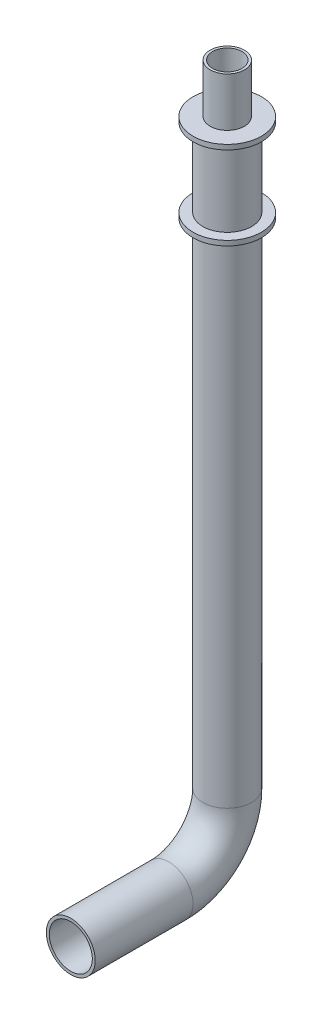
SolidWorks part; units mm, degrees
material "AISI 316 Stainless Steel Sheet (SS)"
ref_plane "Front Plane" through (0, 0, 0) normal (0, 0, 1) x (1, 0, 0)
ref_plane "Top Plane" through (0, 0, 0) normal (0, 1, 0) x (1, 0, 0)
ref_plane "Right Plane" through (0, 0, 0) normal (1, 0, 0) x (0, 0, -1)
sketch "Sketch2" plane through (0, 0, 0) normal (1, 0, 0) x (0, 0, -1)
  line L0 (-160, 0) -> (-60, 0)
  line L1 (0, 60) -> (0, 650)
  arc A0 (-60, 0) -> (0, 60) centre (-60, 60) ccw
  point P6 (0, 0)
  dimension "D3" = 60
  dimension "D1" = 650
  dimension "D2" = 160
ref_plane "Plane1" through (0, 650, 0) normal (0, 1, 0) x (1, 0, 0)
sketch "Sketch9" plane through (0, 650, 0) normal (0, 1, 0) x (1, 0, 0)
  circle A0 centre (0, 0) radius 25
  dimension "D1" = 50
sweep "Sweep-Thin1" add profiles "Sketch9" path "Sketch2" parameters "D1"=3
sketch "Sketch10" plane through (0, 650, 0) normal (0, 1, 0) x (1, 0, 0)
  circle A0 centre (0, 0) radius 35
  dimension "D1" = 70
extrude "Boss-Extrude1" add sketch "Sketch10" along normal blind 5
sketch "Sketch11" plane through (0, 655, 0) normal (0, 1, 0) x (1, 0, 0)
  circle A0 centre (0, 0) radius 17.5
  dimension "D1" = 35
extrude "Extrude-Thin1" add sketch "Sketch11" along normal blind 50 thin thin type one direction reverse wall 2.5
ref_plane "Plane2" through (0, 610, 0) normal (0, 1, 0) x (1, 0, 0)
mirror "Mirror1" about plane through (0, 610, 0) normal (0, 1, 0) of "Boss-Extrude1"
